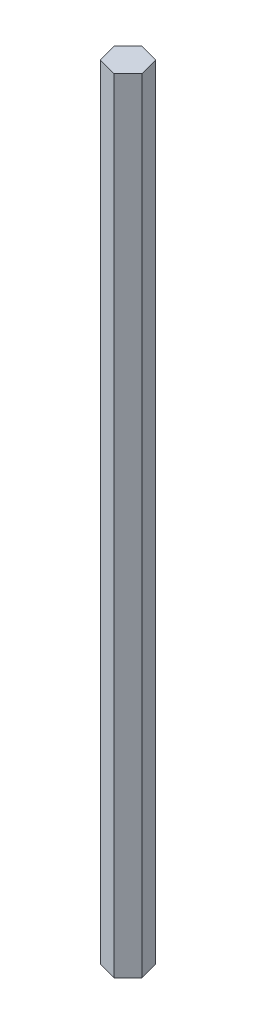
SolidWorks part; units mm, degrees
ref_plane "Front Plane" through (0, 0, 0) normal (0, 0, 1) x (1, 0, 0)
ref_plane "Top Plane" through (0, 0, 0) normal (0, 1, 0) x (1, 0, 0)
ref_plane "Right Plane" through (0, 0, 0) normal (1, 0, 0) x (0, 0, -1)
sketch "Sketch1" plane through (0, 0, 0) normal (0, 1, 0) x (1, 0, 0)
  line L1 (4.9386, 4.9386) -> (-1.8076, 6.7462)
  line L2 (-1.8076, 6.7462) -> (-6.7462, 1.8076)
  line L3 (-6.7462, 1.8076) -> (-4.9386, -4.9386)
  line L4 (-4.9386, -4.9386) -> (1.8076, -6.7462)
  line L5 (1.8076, -6.7462) -> (6.7462, -1.8076)
  line L6 (6.7462, -1.8076) -> (4.9386, 4.9386)
  circle A0 centre (0, 0) radius 6.0485 construction
  dimension "D1" = 6.7462
  dimension "D2" = 6.7462
extrude "Boss-Extrude1" add sketch "Sketch1" along normal blind 279.4
